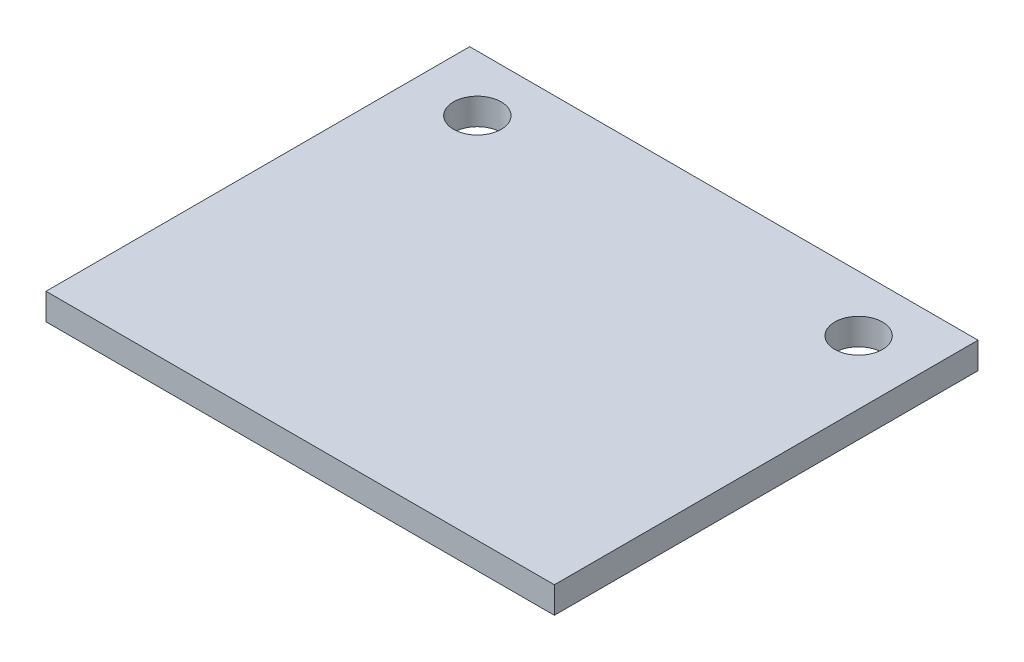
SolidWorks part; units mm, degrees
material "Pine"
ref_plane "Front Plane" through (0, 0, 0) normal (0, 0, 1) x (1, 0, 0)
ref_plane "Top Plane" through (0, 0, 0) normal (0, 1, 0) x (1, 0, 0)
ref_plane "Right Plane" through (0, 0, 0) normal (1, 0, 0) x (0, 0, -1)
sketch "Sketch1" plane through (0, 0, 0) normal (0, 1, 0) x (1, 0, 0)
  line L0 (114.3, 133.35) -> (114.3, 87.1807) construction
  line L1 (-152.4, 133.35) -> (152.4, 133.35)
  line L2 (-152.4, 133.35) -> (-152.4, -133.35)
  line L3 (-152.4, -133.35) -> (152.4, -133.35)
  line L4 (152.4, 133.35) -> (152.4, -133.35)
  line L5 (-152.4, 133.35) -> (152.4, -133.35) construction
  line L6 (-152.4, -133.35) -> (152.4, 133.35) construction
  line L7 (114.3, 87.1807) -> (152.4, 87.1807) construction
  line L8 (-114.3, 133.35) -> (-114.3, 87.1807) construction
  line L9 (-114.3, 87.1807) -> (-152.4, 87.1807) construction
  line L10 (-114.3, 87.1807) -> (-114.3, 49.2856) construction
  line L11 (114.3, 87.1807) -> (114.3, 49.2856) construction
  circle A0 centre (-114.3, 87.1807) radius 14.2875
  circle A1 centre (114.3, 87.1807) radius 14.2875
  point P0 (0, 0)
  dimension "D3" = 28.575
  dimension "D1" = 266.7
  dimension "D2" = 304.8
  dimension "D5" = 228.6
extrude "Boss-Extrude1" add sketch "Sketch1" along normal blind 15.875
sketch "Sketch2" plane through (0, 15.875, 0) normal (0, 1, 0) x (1, 0, 0)
  line L0 (152.4, -133.35) -> (152.4, 133.35) construction
  line L1 (-152.4, 133.35) -> (152.4, 133.35)
  line L2 (-152.4, 133.35) -> (-152.4, 120.65)
  line L3 (-152.4, 120.65) -> (152.4, 120.65)
  line L4 (152.4, 133.35) -> (152.4, 120.65)
  dimension "D1" = 12.7
extrude "Cut-Extrude1" cut sketch "Sketch2" against normal through all
